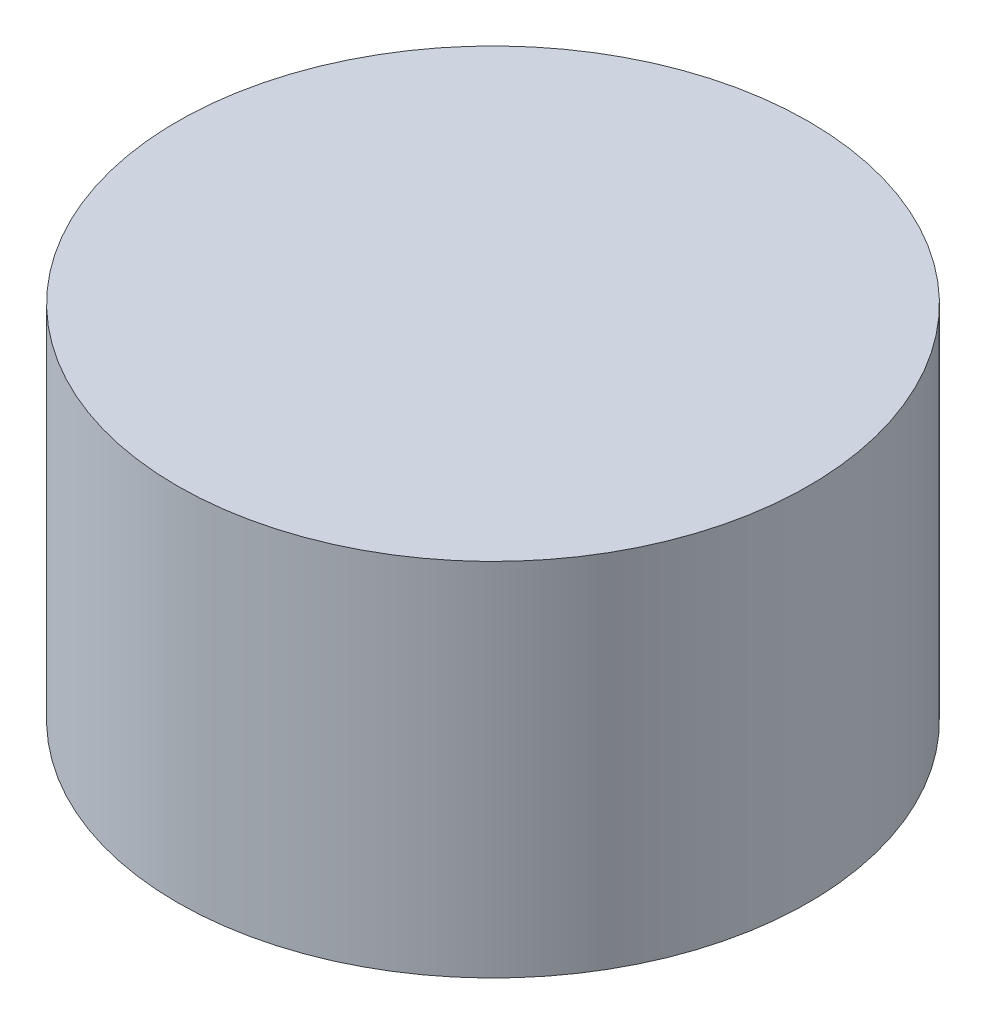
SolidWorks part; units mm, degrees
ref_plane "Plano frontal" through (0, 0, 0) normal (0, 0, 1) x (1, 0, 0)
ref_plane "Plano superior" through (0, 0, 0) normal (0, 1, 0) x (1, 0, 0)
ref_plane "Plano direito" through (0, 0, 0) normal (1, 0, 0) x (0, 0, -1)
sketch "Esboço1" plane through (0, 0, 0) normal (0, 1, 0) x (1, 0, 0)
  circle A0 centre (0, 0) radius 45.5
  dimension "D1" = 91
extrude "Ressalto-extrusão1" add sketch "Esboço1" along normal blind 2
sketch "Esboço2" plane through (0, 0, 0) normal (0, -1, 0) x (1, 0, 0)
  circle A0 centre (0, 0) radius 43.5
  circle A2 centre (0, 0) radius 45.5
extrude "Ressalto-extrusão2" add sketch "Esboço2" along normal blind 50
